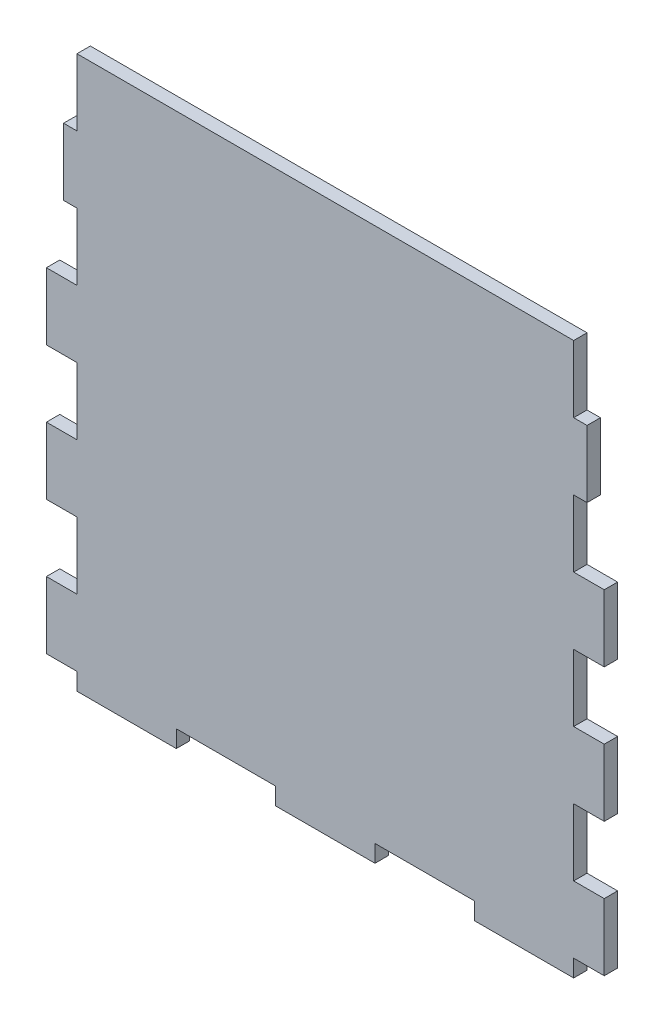
SolidWorks part; units mm, degrees
ref_plane "Front Plane" through (0, 0, 0) normal (0, 0, 1) x (1, 0, 0)
ref_plane "Top Plane" through (0, 0, 0) normal (0, 1, 0) x (1, 0, 0)
ref_plane "Right Plane" through (0, 0, 0) normal (1, 0, 0) x (0, 0, -1)
sketch "Sketch1" plane through (0, 0, 0) normal (0, 0, 1) x (1, 0, 0)
  line L1 (0, 0) -> (65, 0)
  line L2 (0, 0) -> (0, 70)
  line L3 (0, 70) -> (65, 70)
  line L4 (65, 0) -> (65, 70)
  dimension "D1" = 65
  dimension "D2" = 70
extrude "Boss-Extrude1" add sketch "Sketch1" along normal blind 1.75
sketch "Sketch2" plane through (0, 0, 1.75) normal (0, 0, 1) x (1, 0, 0)
  line L0 (-4, 8.75) -> (-4, 17.5) construction
  line L1 (0, 0) -> (-4, 0)
  line L2 (0, 0) -> (0, 8.75)
  line L3 (0, 8.75) -> (-4, 8.75)
  line L4 (-4, 0) -> (-4, 8.75)
  line L5 (0, 17.5) -> (-4, 17.5)
  line L6 (0, 17.5) -> (0, 26.25)
  line L7 (0, 26.25) -> (-4, 26.25)
  line L8 (-4, 17.5) -> (-4, 26.25)
  line L9 (-4, 26.25) -> (-4, 35) construction
  line L10 (0, 35) -> (-4, 35)
  line L11 (0, 35) -> (0, 43.75)
  line L12 (0, 43.75) -> (-4, 43.75)
  line L13 (-4, 35) -> (-4, 43.75)
  line L14 (-4, 43.75) -> (-4, 52.5) construction
  line L15 (0, 52.5) -> (-4, 52.5)
  line L16 (0, 52.5) -> (0, 61.25)
  line L17 (0, 61.25) -> (-4, 61.25)
  line L18 (-4, 52.5) -> (-4, 61.25)
  line L19 (-4, 61.25) -> (-4, 70) construction
  line L20 (65, 70) -> (0, 70) construction
  line L21 (32.5, 0) -> (32.5, 70) construction
  line L22 (0, 0) -> (65, 0) construction
  line L23 (69, 61.25) -> (69, 70) construction
  line L24 (69, 43.75) -> (69, 52.5) construction
  line L25 (69, 26.25) -> (69, 35) construction
  line L26 (69, 8.75) -> (69, 17.5) construction
  line L27 (69, 52.5) -> (69, 61.25)
  line L28 (65, 61.25) -> (69, 61.25)
  line L29 (65, 52.5) -> (65, 61.25)
  line L30 (65, 52.5) -> (69, 52.5)
  line L31 (69, 35) -> (69, 43.75)
  line L32 (65, 43.75) -> (69, 43.75)
  line L33 (65, 35) -> (65, 43.75)
  line L34 (65, 35) -> (69, 35)
  line L35 (69, 17.5) -> (69, 26.25)
  line L36 (65, 26.25) -> (69, 26.25)
  line L37 (65, 17.5) -> (65, 26.25)
  line L38 (65, 17.5) -> (69, 17.5)
  line L39 (69, 0) -> (69, 8.75)
  line L40 (65, 8.75) -> (69, 8.75)
  line L41 (65, 0) -> (65, 8.75)
  line L42 (65, 0) -> (69, 0)
  line L43 (13, -2.25) -> (26, -2.25) construction
  line L44 (0, 0) -> (13, 0)
  line L45 (0, 0) -> (0, -2.25)
  line L46 (0, -2.25) -> (13, -2.25)
  line L47 (13, 0) -> (13, -2.25)
  line L48 (26, 0) -> (26, -2.25)
  line L49 (26, -2.25) -> (39, -2.25)
  line L50 (39, 0) -> (39, -2.25)
  line L51 (39, -2.25) -> (52, -2.25) construction
  line L52 (26, 0) -> (39, 0)
  line L53 (52, 0) -> (52, -2.25)
  line L54 (52, -2.25) -> (65, -2.25)
  line L55 (65, 0) -> (65, -2.25)
  line L56 (65, -2.25) -> (78, -2.25) construction
  line L57 (52, 0) -> (65, 0)
  line M26 (0, 70) -> (0, 0)
  line M27 (0, 0) -> (65, 0)
  line M28 (65, 0) -> (65, 70)
  dimension "D2" = 4
  dimension "D4" = 2.25
  dimension "D1" = 4
  dimension "D3" = 3
extrude "Boss-Extrude2" add sketch "Sketch2" against normal up to surface (1.75 mm away) contours L34 L31 L32 M28 | L38 L35 L36 M28 | L42 L39 L40 M28 | L47 L45 L46 M27 | L4 L1 L3 M26 | L8 L5 L7 M26 | L18 L15 L17 M26 | L29 L28 L27 L30 | L57 L53 L54 L55 | L49 L50 L52 L48 | L13 L12 L11 L10 up to face at (32.5, 35, 0)
sketch "Sketch3" plane through (0, 0, 0) normal (0, 0, -1) x (-1, 0, 0)
  line L0 (-65, 52.5) -> (-69, 52.5) construction
  line L1 (-69, 61.25) -> (-66.75, 61.25)
  line L2 (-69, 61.25) -> (-69, 52.5)
  line L3 (-69, 52.5) -> (-66.75, 52.5)
  line L4 (-66.75, 61.25) -> (-66.75, 52.5)
  line L5 (0, 52.5) -> (4, 52.5) construction
  line L6 (4, 61.25) -> (1.75, 61.25)
  line L7 (4, 61.25) -> (4, 52.5)
  line L8 (4, 52.5) -> (1.75, 52.5)
  line L9 (1.75, 61.25) -> (1.75, 52.5)
  dimension "D1" = 2.25
extrude "Cut-Extrude1" cut sketch "Sketch3" against normal through all
equation "\"D1@Boss-Extrude1\"=\"thick\""
equation "\"D2@Sketch2\"=\"thick\"*2 + \"veneer_thickness\""
equation "\"D4@Sketch2\"=\"thick\" + \"veneer_thickness\""
equation "\"D1@Sketch3\"=\"thick\"+\"veneer_thickness\""
equation "\"veneer_thickness\"= 0.5mm"
equation "\"thick\"= 1.75mm"
